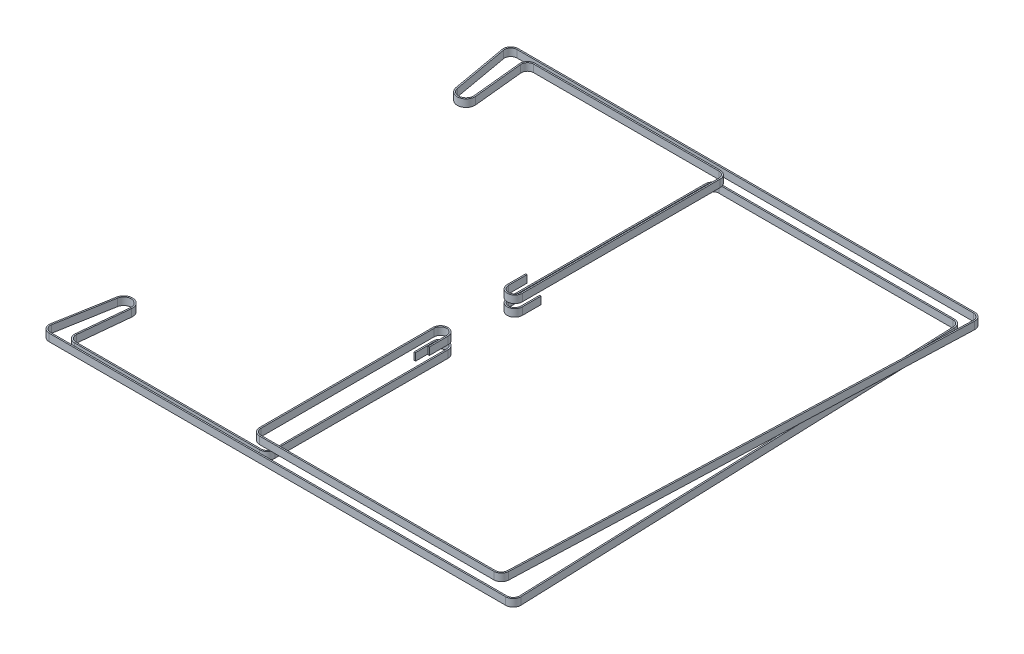
SolidWorks part; units mm, degrees
ref_plane "Alzado" through (0, 0, 0) normal (0, 0, 1) x (1, 0, 0)
ref_plane "Planta" through (0, 0, 0) normal (0, 1, 0) x (1, 0, 0)
ref_plane "Vista lateral" through (0, 0, 0) normal (1, 0, 0) x (0, 0, -1)
sketch "Croquis2" plane through (0, 336.5, 0) normal (0, 1, 0) x (1, 0, 0)
  line L0 (-159.9077, -136.9518) -> (-167.9231, -182.1265) construction
  line L1 (-163, -188) -> (205, -188) construction
  line L2 (-152.0696, -178.8915) -> (-148.0299, -138.5985) construction
  line L3 (3.2461, -185.6) -> (-146, -185.6) construction
  line L4 (9.3461, -179.5) -> (9.3461, -39.9945) construction
  line L5 (209.9968, -182.8208) -> (196.9968, 179.6792) construction
  line L6 (192, 184.5) -> (3.2461, 184.5) construction
  line L7 (-1.7539, 179.5) -> (-1.7539, 20.0055) construction
  line L8 (-159.9077, -136.9518) -> (-167.9231, -182.1265)
  line L9 (-163, -188) -> (205, -188)
  line L10 (-152.0696, -178.8915) -> (-148.0299, -138.5985)
  line L11 (3.2461, -185.6) -> (-146, -185.6)
  line L12 (9.3461, -179.5) -> (9.3461, -39.9945)
  line L13 (209.9968, -182.8208) -> (196.9968, 179.6792)
  line L14 (192, 184.5) -> (3.2461, 184.5)
  line L15 (-1.7539, 179.5) -> (-1.7539, 20.0055)
  line L17 (-2.8539, -39.9945) -> (-2.8539, -54.9945) construction
  line L19 (-2.8539, -39.9945) -> (-2.8539, -54.9945)
  line L21 (8.2461, 20.0055) -> (8.2461, 35.0055) construction
  line L23 (8.2461, 20.0055) -> (8.2461, 35.0055)
  arc A0 (-148.0299, -138.5985) -> (-159.9077, -136.9518) centre (-154, -138) ccw construction
  arc A3 (-148.0299, -138.5985) -> (-159.9077, -136.9518) centre (-154, -138) ccw
  arc A4 (-167.9231, -182.1265) -> (-163, -188) centre (-163, -183) ccw construction
  arc A5 (-152.0696, -178.8915) -> (-146, -185.6) centre (-146, -179.5) ccw construction
  arc A6 (3.2461, -185.6) -> (9.3461, -179.5) centre (3.2461, -179.5) ccw construction
  arc A7 (205, -188) -> (209.9968, -182.8208) centre (205, -183) ccw construction
  arc A8 (196.9968, 179.6792) -> (192, 184.5) centre (192, 179.5) ccw construction
  arc A9 (3.2461, 184.5) -> (-1.7539, 179.5) centre (3.2461, 179.5) ccw construction
  arc A10 (-167.9231, -182.1265) -> (-163, -188) centre (-163, -183) ccw
  arc A11 (-152.0696, -178.8915) -> (-146, -185.6) centre (-146, -179.5) ccw
  arc A12 (3.2461, -185.6) -> (9.3461, -179.5) centre (3.2461, -179.5) ccw
  arc A13 (205, -188) -> (209.9968, -182.8208) centre (205, -183) ccw
  arc A14 (196.9968, 179.6792) -> (192, 184.5) centre (192, 179.5) ccw
  arc A15 (3.2461, 184.5) -> (-1.7539, 179.5) centre (3.2461, 179.5) ccw
  arc A16 (9.3461, -39.9945) -> (-2.8539, -39.9945) centre (3.2461, -39.9945) ccw construction
  arc A17 (9.3461, -39.9945) -> (-2.8539, -39.9945) centre (3.2461, -39.9945) ccw
  arc A20 (-1.7539, 20.0055) -> (8.2461, 20.0055) centre (3.2461, 20.0055) ccw construction
  arc A21 (-1.7539, 20.0055) -> (8.2461, 20.0055) centre (3.2461, 20.0055) ccw
ref_plane "Plano1" through (0, 0, 54.9945) normal (0, 0, 1) x (1, 0, 0)
sketch "Croquis3" plane through (0, 0, 54.9945) normal (0, 0, 1) x (1, 0, 0)
  line L1 (-1.7539, 336.5) -> (-2.8539, 336.5)
  line L2 (-1.7539, 336.5) -> (-1.7539, 342.5)
  line L3 (-1.7539, 342.5) -> (-2.8539, 342.5)
  line L4 (-2.8539, 336.5) -> (-2.8539, 342.5)
  dimension "D1" = 6
  dimension "D2" = 1.1
sweep "Barrer1" add profiles "Croquis3" path "Croquis2"
sketch "Croquis4" plane through (0, 346, 0) normal (0, 1, 0) x (1, 0, 0)
  line L0 (-152.0696, 178.8915) -> (-148.0299, 138.5985) construction
  line L1 (-167.9231, 182.1265) -> (-159.9077, 136.9518) construction
  line L2 (-163, 188) -> (205, 188) construction
  line L3 (3.2461, 185.6) -> (-146, 185.6) construction
  line L4 (9.3461, 179.5) -> (9.3461, 20.0055) construction
  line L5 (209.9968, 182.8208) -> (196.9968, -179.6792) construction
  line L6 (192, -184.5) -> (3.2461, -184.5) construction
  line L7 (-1.7539, -179.5) -> (-1.7539, -39.9945) construction
  line L8 (-152.0696, 178.8915) -> (-148.0299, 138.5985)
  line L9 (-167.9231, 182.1265) -> (-159.9077, 136.9518)
  line L10 (-163, 188) -> (205, 188)
  line L11 (3.2461, 185.6) -> (-146, 185.6)
  line L12 (9.3461, 179.5) -> (9.3461, 20.0055)
  line L13 (209.9968, 182.8208) -> (196.9968, -179.6792)
  line L14 (192, -184.5) -> (3.2461, -184.5)
  line L15 (-1.7539, -179.5) -> (-1.7539, -39.9945)
  line L16 (-2.8539, 20.0055) -> (-2.8539, 35.0055) construction
  line L19 (8.2461, -39.9945) -> (8.2461, -54.9945) construction
  line L20 (-2.8539, 20.0055) -> (-2.8539, 35.0055)
  line L23 (8.2461, -39.9945) -> (8.2461, -54.9945)
  arc A0 (-159.9077, 136.9518) -> (-148.0299, 138.5985) centre (-154, 138) ccw construction
  arc A1 (-163, 188) -> (-167.9231, 182.1265) centre (-163, 183) ccw construction
  arc A2 (-146, 185.6) -> (-152.0696, 178.8915) centre (-146, 179.5) ccw construction
  arc A3 (9.3461, 179.5) -> (3.2461, 185.6) centre (3.2461, 179.5) ccw construction
  arc A4 (209.9968, 182.8208) -> (205, 188) centre (205, 183) ccw construction
  arc A5 (192, -184.5) -> (196.9968, -179.6792) centre (192, -179.5) ccw construction
  arc A6 (-1.7539, -179.5) -> (3.2461, -184.5) centre (3.2461, -179.5) ccw construction
  arc A7 (-159.9077, 136.9518) -> (-148.0299, 138.5985) centre (-154, 138) ccw
  arc A8 (-163, 188) -> (-167.9231, 182.1265) centre (-163, 183) ccw
  arc A9 (-146, 185.6) -> (-152.0696, 178.8915) centre (-146, 179.5) ccw
  arc A10 (9.3461, 179.5) -> (3.2461, 185.6) centre (3.2461, 179.5) ccw
  arc A11 (209.9968, 182.8208) -> (205, 188) centre (205, 183) ccw
  arc A12 (192, -184.5) -> (196.9968, -179.6792) centre (192, -179.5) ccw
  arc A13 (-1.7539, -179.5) -> (3.2461, -184.5) centre (3.2461, -179.5) ccw
  arc A18 (-2.8539, 20.0055) -> (9.3461, 20.0055) centre (3.2461, 20.0055) ccw construction
  arc A19 (-2.8539, 20.0055) -> (9.3461, 20.0055) centre (3.2461, 20.0055) ccw
  arc A20 (8.2461, -39.9945) -> (-1.7539, -39.9945) centre (3.2461, -39.9945) ccw construction
  arc A21 (8.2461, -39.9945) -> (-1.7539, -39.9945) centre (3.2461, -39.9945) ccw
ref_plane "Plano2" through (0, 0, -35.0055) normal (0, 0, 1) x (1, 0, 0)
sketch "Croquis5" plane through (0, 0, -35.0055) normal (0, 0, 1) x (1, 0, 0)
  line L1 (-1.7539, 346) -> (-2.8539, 346)
  line L2 (-1.7539, 346) -> (-1.7539, 352)
  line L3 (-1.7539, 352) -> (-2.8539, 352)
  line L4 (-2.8539, 346) -> (-2.8539, 352)
  dimension "D1" = 6
  dimension "D2" = 1.1
sweep "Barrer2" add profiles "Croquis5" path "Croquis4"
